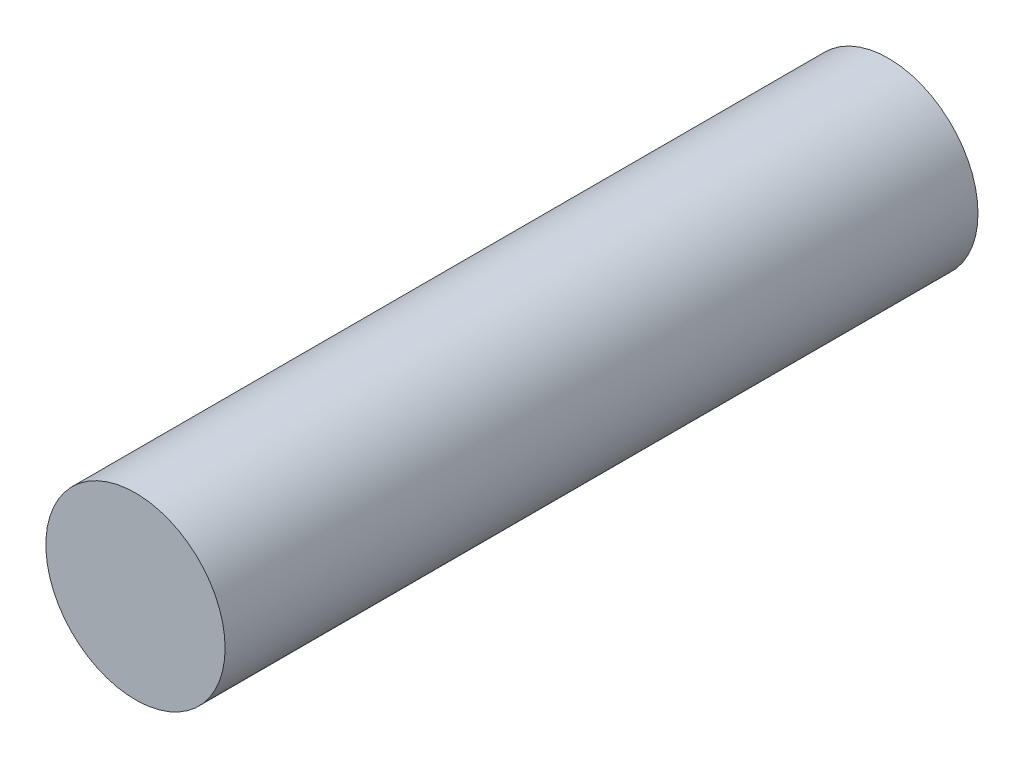
SolidWorks part; units mm, degrees
ref_plane "Front" through (0, 0, 0) normal (0, 0, 1) x (1, 0, 0)
ref_plane "Top" through (0, 0, 0) normal (0, 1, 0) x (1, 0, 0)
ref_plane "Right" through (0, 0, 0) normal (1, 0, 0) x (0, 0, -1)
sketch "Эскиз1" plane through (0, 0, 0) normal (0, 0, 1) x (1, 0, 0)
  circle A0 centre (0, 0) radius 3.75
  dimension "D1" = 7.5
extrude "Бобышка-Вытянуть1" add sketch "Эскиз1" along normal blind 31.5
